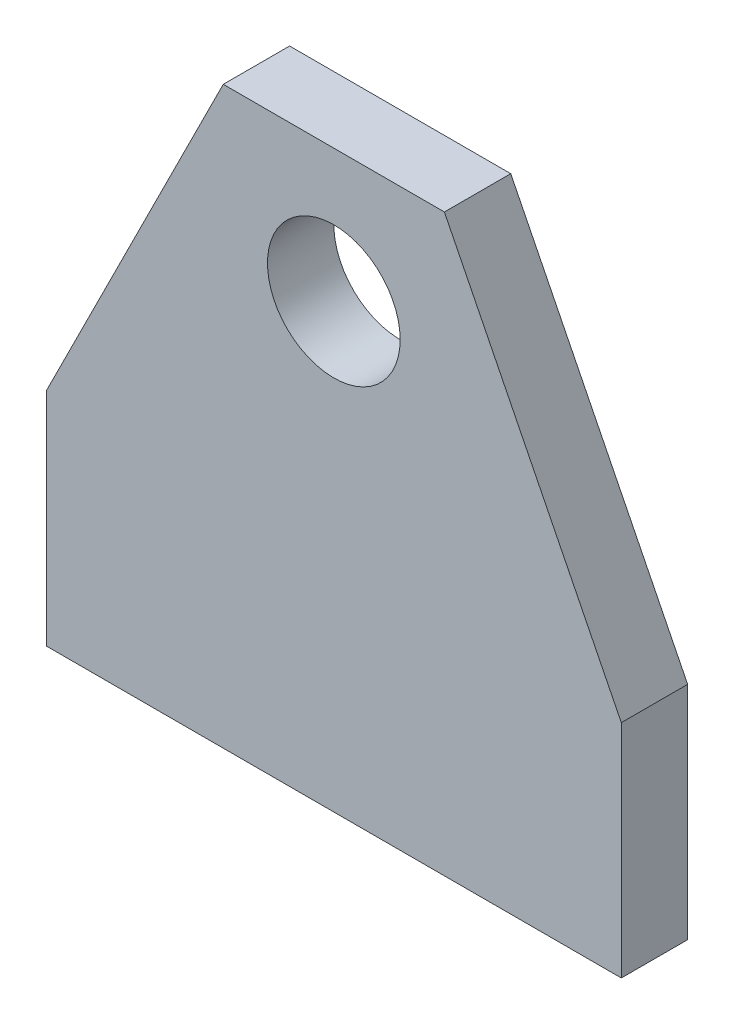
SolidWorks part; units mm, degrees
material "PW20:29:Sc:0:"
ref_plane "Front" through (0, 0, 0) normal (0, 0, 1) x (1, 0, 0)
ref_plane "Top" through (0, 0, 0) normal (0, 1, 0) x (1, 0, 0)
ref_plane "Right" through (0, 0, 0) normal (1, 0, 0) x (0, 0, -1)
sketch "Sketch1" plane through (0, 0, 0) normal (0, 0, 1) x (1, 0, 0)
  line L0 (0, 0) -> (0, 74.0054) construction
  line L1 (-15.875, 82.55) -> (15.875, 82.55)
  line L2 (15.875, 82.55) -> (41.275, 31.75)
  line L3 (-15.875, 82.55) -> (-41.275, 31.75)
  line L4 (41.275, 31.75) -> (41.275, 0)
  line L5 (-41.275, 31.75) -> (-41.275, 0)
  line L6 (41.275, 0) -> (-41.275, 0)
  line L7 (0, 0) -> (99.2345, 0) construction
  circle A0 centre (0, 63.5) radius 9.525
  dimension "D6" = 19.05
  dimension "D1" = 82.55
  dimension "D2" = 82.55
  dimension "D3" = 50.8
  dimension "D4" = 25.4
  dimension "D5" = 63.5
extrude "Base-Extrude" add sketch "Sketch1" along normal blind 9.525
